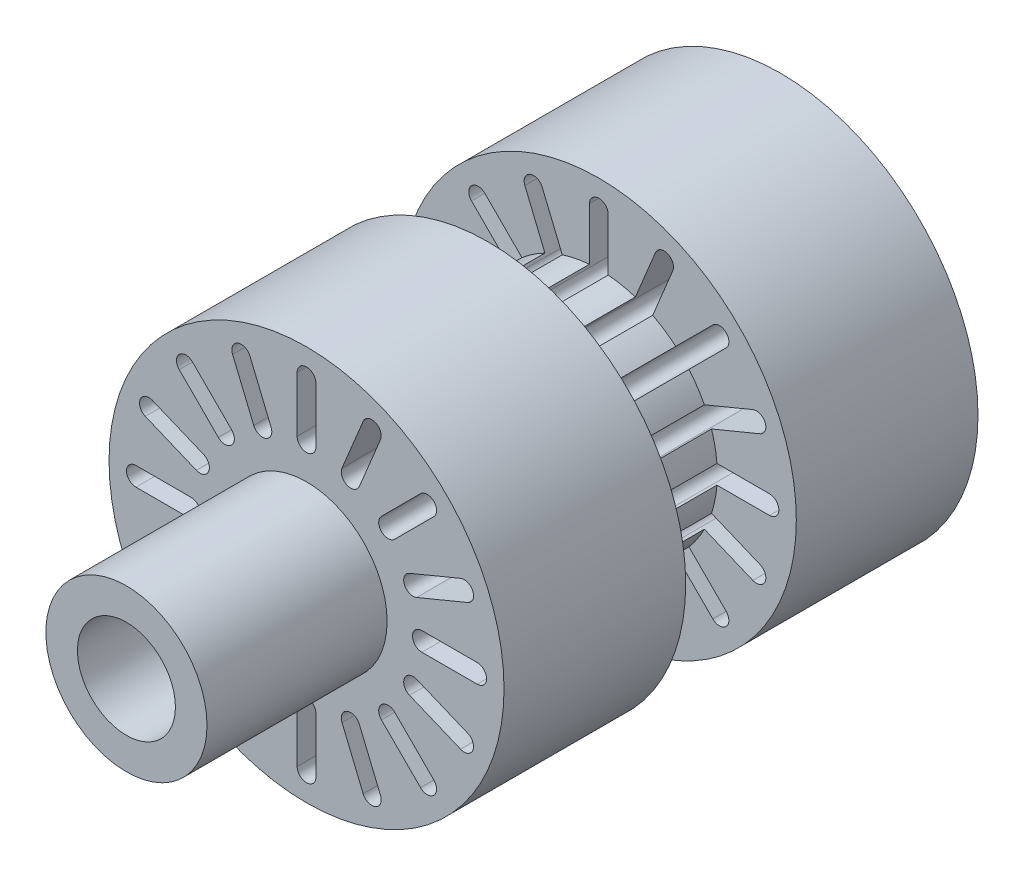
SolidWorks part; units mm, degrees
ref_plane "Front Plane" through (0, 0, 0) normal (0, 0, 1) x (1, 0, 0)
ref_plane "Top Plane" through (0, 0, 0) normal (0, 1, 0) x (1, 0, 0)
ref_plane "Right Plane" through (0, 0, 0) normal (1, 0, 0) x (0, 0, -1)
sketch "Sketch1" plane through (0, 0, 0) normal (1, 0, 0) x (0, 0, -1)
  line L0 (-15, 0) -> (15, 0)
  line L1 (-15, 5.1) -> (-15, 12.5)
  line L2 (-15, 0) -> (15, 0)
  line L3 (-15, 2) -> (-15, 3.1)
  line L4 (-15, 12.5) -> (-3.5, 12.5)
  line L5 (15, 6) -> (15, 12.5)
  line L6 (15, 0) -> (3.6, 0)
  line L8 (15, 6) -> (3.6, 6)
  line L9 (3.6, 3.1) -> (3.6, 6)
  line L10 (3.5, 12.5) -> (15, 12.5)
  line L12 (3.5, 12.5) -> (3.5, 7.5)
  line L13 (3.5, 7.5) -> (-3.5, 7.5)
  line L14 (-3.5, 12.5) -> (-3.5, 7.5)
  line L19 (3.6, 0) -> (-15, 0)
  line L21 (3.6, 3.1) -> (-15, 3.1)
  line L22 (-15, 2) -> (-15, 3.1)
  line L23 (-15, 3.1) -> (-26.4, 3.1)
  line L25 (-15, 5.1) -> (-26.4, 5.1)
  line L26 (-26.4, 3.1) -> (-26.4, 5.1)
  point P4 (0, 0)
  point P13 (0, 12.5)
  dimension "D1" = 30
  dimension "D2" = 12.5
  dimension "D3" = 11.4
  dimension "D4" = 6
  dimension "D5" = 5
  dimension "D6" = 3.1
  dimension "D7" = 11.4
  dimension "D8" = 2
  dimension "D9" = 1.5
revolve "Revolve1" add sketch "Sketch1" angle 360 about L0
sketch "Sketch2" plane through (0, 0, -15) normal (0, 0, -1) x (-1, 0, 0)
  line L0 (0, 6) -> (0, 12.5) construction
  line L1 (0, 12.5) -> (0, 11.3) construction
  line L2 (0, 6) -> (0, 5.8) construction
  line L3 (0, 11.3) -> (0, 10.8) construction
  line L4 (0, 5.8) -> (0, 7.3) construction
  line L5 (0, 10.8) -> (0, 7.3) construction
  line L6 (0.5941, 10.8) -> (0.5941, 7.3)
  line L7 (-0.5941, 10.8) -> (-0.5941, 7.3)
  line L8 (3.5841, 10.2053) -> (2.2447, 6.9717)
  line L9 (4.6819, 9.7505) -> (3.3425, 6.517)
  line L10 (4.133, 9.9779) -> (2.7936, 6.7443) construction
  line L11 (7.2166, 8.0569) -> (4.7418, 5.582)
  line L12 (8.0569, 7.2166) -> (5.582, 4.7418)
  line L13 (7.6368, 7.6368) -> (5.1619, 5.1619) construction
  line L14 (9.7505, 4.6819) -> (6.517, 3.3425)
  line L15 (10.2053, 3.5841) -> (6.9717, 2.2447)
  line L16 (9.9779, 4.133) -> (6.7443, 2.7936) construction
  line L17 (10.8, 0.5941) -> (7.3, 0.5941)
  line L18 (10.8, -0.5941) -> (7.3, -0.5941)
  line L19 (10.8, 0) -> (7.3, 0) construction
  line L20 (10.2053, -3.5841) -> (6.9717, -2.2447)
  line L21 (9.7505, -4.6819) -> (6.517, -3.3425)
  line L22 (9.9779, -4.133) -> (6.7443, -2.7936) construction
  line L23 (8.0569, -7.2166) -> (5.582, -4.7418)
  line L24 (7.2166, -8.0569) -> (4.7418, -5.582)
  line L25 (7.6368, -7.6368) -> (5.1619, -5.1619) construction
  line L26 (4.6819, -9.7505) -> (3.3425, -6.517)
  line L27 (3.5841, -10.2053) -> (2.2447, -6.9717)
  line L28 (4.133, -9.9779) -> (2.7936, -6.7443) construction
  line L29 (0.5941, -10.8) -> (0.5941, -7.3)
  line L30 (-0.5941, -10.8) -> (-0.5941, -7.3)
  line L31 (0, -10.8) -> (0, -7.3) construction
  line L32 (-3.5841, -10.2053) -> (-2.2447, -6.9717)
  line L33 (-4.6819, -9.7505) -> (-3.3425, -6.517)
  line L34 (-4.133, -9.9779) -> (-2.7936, -6.7443) construction
  line L35 (-7.2166, -8.0569) -> (-4.7418, -5.582)
  line L36 (-8.0569, -7.2166) -> (-5.582, -4.7418)
  line L37 (-7.6368, -7.6368) -> (-5.1619, -5.1619) construction
  line L38 (-9.7505, -4.6819) -> (-6.517, -3.3425)
  line L39 (-10.2053, -3.5841) -> (-6.9717, -2.2447)
  line L40 (-9.9779, -4.133) -> (-6.7443, -2.7936) construction
  line L41 (-10.8, -0.5941) -> (-7.3, -0.5941)
  line L42 (-10.8, 0.5941) -> (-7.3, 0.5941)
  line L43 (-10.8, 0) -> (-7.3, 0) construction
  line L44 (-10.2053, 3.5841) -> (-6.9717, 2.2447)
  line L45 (-9.7505, 4.6819) -> (-6.517, 3.3425)
  line L46 (-9.9779, 4.133) -> (-6.7443, 2.7936) construction
  line L47 (-8.0569, 7.2166) -> (-5.582, 4.7418)
  line L48 (-7.2166, 8.0569) -> (-4.7418, 5.582)
  line L49 (-7.6368, 7.6368) -> (-5.1619, 5.1619) construction
  line L50 (-4.6819, 9.7505) -> (-3.3425, 6.517)
  line L51 (-3.5841, 10.2053) -> (-2.2447, 6.9717)
  line L52 (-4.133, 9.9779) -> (-2.7936, 6.7443) construction
  circle A0 centre (0, 0) radius 6 construction
  circle A1 centre (0, 0) radius 12.5 construction
  arc A2 (0.5941, 10.8) -> (-0.5941, 10.8) centre (0, 10.8) ccw
  arc A3 (-0.5941, 7.3) -> (0.5941, 7.3) centre (0, 7.3) ccw
  arc A4 (4.6819, 9.7505) -> (3.5841, 10.2053) centre (4.133, 9.9779) ccw
  arc A5 (2.2447, 6.9717) -> (3.3425, 6.517) centre (2.7936, 6.7443) ccw
  arc A6 (8.0569, 7.2166) -> (7.2166, 8.0569) centre (7.6368, 7.6368) ccw
  arc A7 (4.7418, 5.582) -> (5.582, 4.7418) centre (5.1619, 5.1619) ccw
  arc A8 (10.2053, 3.5841) -> (9.7505, 4.6819) centre (9.9779, 4.133) ccw
  arc A9 (6.517, 3.3425) -> (6.9717, 2.2447) centre (6.7443, 2.7936) ccw
  arc A10 (10.8, -0.5941) -> (10.8, 0.5941) centre (10.8, 0) ccw
  arc A11 (7.3, 0.5941) -> (7.3, -0.5941) centre (7.3, 0) ccw
  arc A12 (9.7505, -4.6819) -> (10.2053, -3.5841) centre (9.9779, -4.133) ccw
  arc A13 (6.9717, -2.2447) -> (6.517, -3.3425) centre (6.7443, -2.7936) ccw
  arc A14 (7.2166, -8.0569) -> (8.0569, -7.2166) centre (7.6368, -7.6368) ccw
  arc A15 (5.582, -4.7418) -> (4.7418, -5.582) centre (5.1619, -5.1619) ccw
  arc A16 (3.5841, -10.2053) -> (4.6819, -9.7505) centre (4.133, -9.9779) ccw
  arc A17 (3.3425, -6.517) -> (2.2447, -6.9717) centre (2.7936, -6.7443) ccw
  arc A18 (-0.5941, -10.8) -> (0.5941, -10.8) centre (0, -10.8) ccw
  arc A19 (0.5941, -7.3) -> (-0.5941, -7.3) centre (0, -7.3) ccw
  arc A20 (-4.6819, -9.7505) -> (-3.5841, -10.2053) centre (-4.133, -9.9779) ccw
  arc A21 (-2.2447, -6.9717) -> (-3.3425, -6.517) centre (-2.7936, -6.7443) ccw
  arc A22 (-8.0569, -7.2166) -> (-7.2166, -8.0569) centre (-7.6368, -7.6368) ccw
  arc A23 (-4.7418, -5.582) -> (-5.582, -4.7418) centre (-5.1619, -5.1619) ccw
  arc A24 (-10.2053, -3.5841) -> (-9.7505, -4.6819) centre (-9.9779, -4.133) ccw
  arc A25 (-6.517, -3.3425) -> (-6.9717, -2.2447) centre (-6.7443, -2.7936) ccw
  arc A26 (-10.8, 0.5941) -> (-10.8, -0.5941) centre (-10.8, 0) ccw
  arc A27 (-7.3, -0.5941) -> (-7.3, 0.5941) centre (-7.3, 0) ccw
  arc A28 (-9.7505, 4.6819) -> (-10.2053, 3.5841) centre (-9.9779, 4.133) ccw
  arc A29 (-6.9717, 2.2447) -> (-6.517, 3.3425) centre (-6.7443, 2.7936) ccw
  arc A30 (-7.2166, 8.0569) -> (-8.0569, 7.2166) centre (-7.6368, 7.6368) ccw
  arc A31 (-5.582, 4.7418) -> (-4.7418, 5.582) centre (-5.1619, 5.1619) ccw
  arc A32 (-3.5841, 10.2053) -> (-4.6819, 9.7505) centre (-4.133, 9.9779) ccw
  arc A33 (-3.3425, 6.517) -> (-2.2447, 6.9717) centre (-2.7936, 6.7443) ccw
  point P11 (0, 9.05)
  point P21 (3.4633, 8.3611)
  point P28 (6.3993, 6.3993)
  point P35 (8.3611, 3.4633)
  point P42 (9.05, 0)
  point P49 (8.3611, -3.4633)
  point P56 (6.3993, -6.3993)
  point P63 (3.4633, -8.3611)
  point P70 (0, -9.05)
  point P77 (-3.4633, -8.3611)
  point P84 (-6.3993, -6.3993)
  point P91 (-8.3611, -3.4633)
  point P98 (-9.05, 0)
  point P105 (-8.3611, 3.4633)
  point P112 (-6.3993, 6.3993)
  point P119 (-3.4633, 8.3611)
  dimension "D1" = 1.2
  dimension "D2" = 0.5
  dimension "D3" = 1.5
  dimension "D4" = 16
extrude "Cut-Extrude1" cut sketch "Sketch2" against normal blind 86
